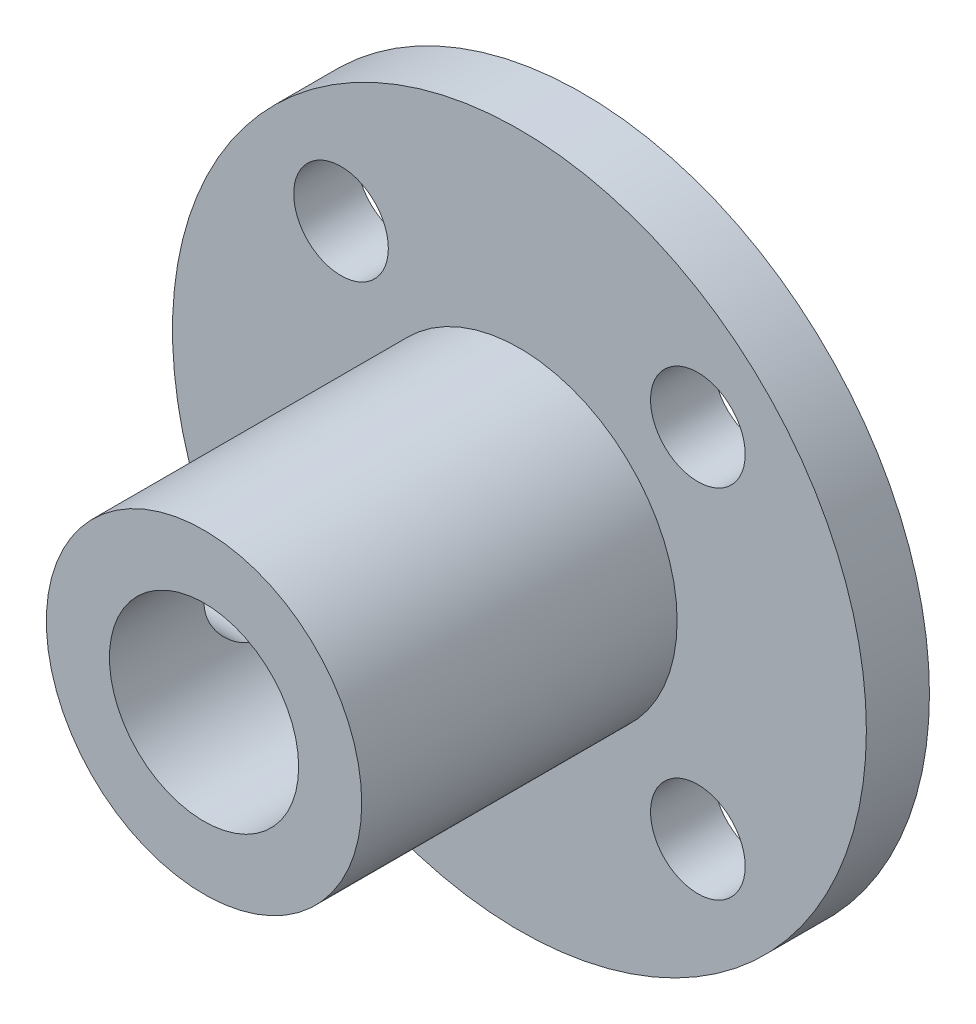
SolidWorks part; units mm, degrees
material "Простая углеродистая сталь"
ref_plane "Front" through (0, 0, 0) normal (0, 0, 1) x (1, 0, 0)
ref_plane "Top" through (0, 0, 0) normal (0, 1, 0) x (1, 0, 0)
ref_plane "Right" through (0, 0, 0) normal (1, 0, 0) x (0, 0, -1)
sketch "Эскиз1" plane through (0, 0, 0) normal (0, 0, 1) x (1, 0, 0)
  circle A0 centre (0, 0) radius 11
extrude "Бобышка-Вытянуть1" add sketch "Эскиз1" along normal blind 2
sketch "Эскиз2" plane through (0, 0, 2) normal (0, 0, 1) x (1, 0, 0)
  circle A0 centre (0, 0) radius 5
extrude "Бобышка-Вытянуть2" add sketch "Эскиз2" along normal blind 10
sketch "Эскиз3" plane through (0, 0, 0) normal (0, 0, 1) x (1, 0, 0)
  circle A0 centre (0, 0) radius 3
extrude "Вырез-Вытянуть2" cut sketch "Эскиз3" along normal through all
sketch "Эскиз4" plane through (0, 0, 2) normal (0, 0, 1) x (1, 0, 0)
  line L0 (0, 0) -> (5.6569, 5.6569) construction
  circle A0 centre (0, 0) radius 8 construction
  circle A1 centre (5.6569, 5.6569) radius 1.5
  circle A2 centre (5.6569, -5.6569) radius 1.5
  circle A3 centre (-5.6569, -5.6569) radius 1.5
  circle A4 centre (-5.6569, 5.6569) radius 1.5
  point P14 (0, 0)
  dimension "D1" = 16
  dimension "D2" = 4
extrude "Вырез-Вытянуть3" cut sketch "Эскиз4" against normal blind 10
sketch "Эскиз5" plane through (0, 0, 0) normal (1, 0, 0) x (0, 0, -1)
  line L0 (0, 0) -> (-7.5, 0) construction
  line L1 (0, -11) -> (0, 11) construction
  circle A0 centre (-7.5, 0) radius 1.5
  dimension "D1" = 3
  dimension "D2" = 7.5
extrude "Вырез-Вытянуть4" cut sketch "Эскиз5" against normal through all
